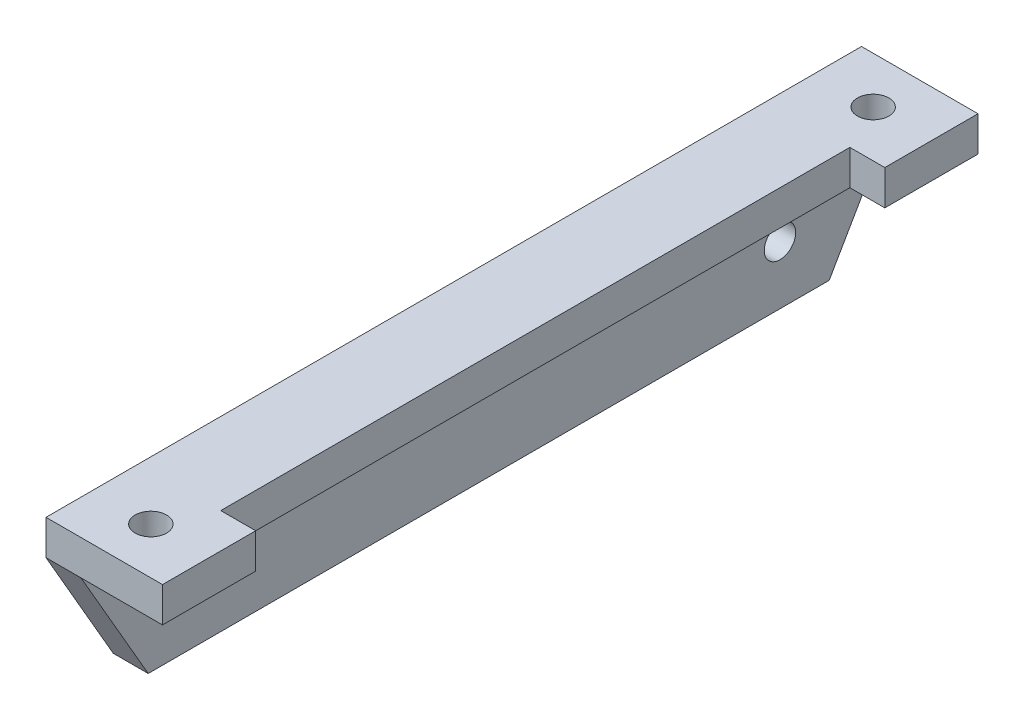
SolidWorks part; units mm, degrees
ref_plane "Front Plane" through (0, 0, 0) normal (0, 0, 1) x (1, 0, 0)
ref_plane "Top Plane" through (0, 0, 0) normal (0, 1, 0) x (1, 0, 0)
ref_plane "Right Plane" through (0, 0, 0) normal (1, 0, 0) x (0, 0, -1)
sketch "Sketch1" plane through (0, 0, 0) normal (0, 1, 0) x (1, 0, 0)
  line L1 (0, -35) -> (10, -35)
  line L2 (0, -35) -> (0, 35)
  line L3 (0, 35) -> (10, 35)
  line L4 (10, -35) -> (10, 35)
  point P4 (0, 0)
  dimension "D1" = 10
  dimension "D2" = 70
extrude "Boss-Extrude1" add sketch "Sketch1" along normal blind 3
sketch "Sketch2" plane through (0, 0, 0) normal (0, -1, 0) x (1, 0, 0)
  line L0 (10, -35) -> (0, -35) construction
  line L1 (0, 35) -> (3, 35)
  line L2 (0, 35) -> (0, -35)
  line L3 (0, -35) -> (3, -35)
  line L4 (3, 35) -> (3, -35)
  dimension "D1" = 3
extrude "Boss-Extrude2" add sketch "Sketch2" along normal blind 10
sketch "Sketch3" plane through (0, 3, 0) normal (0, 1, 0) x (1, 0, 0)
  line L0 (0, 35) -> (0, -35) construction
  circle A0 centre (5, 31) radius 1.35
  circle A1 centre (5, -31) radius 1.35
  dimension "D1" = 62
  dimension "D3" = 2.7
  dimension "D4" = 5
  dimension "D2" = 31
extrude "Cut-Extrude1" cut sketch "Sketch3" against normal through all both and the other way through all
sketch "Sketch4" plane through (3, 0, 0) normal (1, 0, 0) x (0, 0, -1)
  circle A0 centre (25, -5) radius 1.35
  circle A1 centre (-25, -5) radius 1.35
  dimension "D2" = 25
  dimension "D4" = 2.7
  dimension "D1" = 25
  dimension "D3" = 5
extrude "Cut-Extrude2" cut sketch "Sketch4" against normal blind 10
chamfer "Chamfer1" distance 10 angle 30 2 edges at (1.5, -10, -35) (1.5, -10, 35)
sketch "Sketch5" plane through (0, 3, 0) normal (0, 1, 0) x (1, 0, 0)
  line L0 (10, -35) -> (10, 35) construction
  line L1 (10, 27) -> (7, 27)
  line L2 (10, 27) -> (10, -27)
  line L3 (10, -27) -> (7, -27)
  line L4 (7, 27) -> (7, -27)
  circle A0 centre (5, 31) radius 1.35 construction
  circle A1 centre (5, -31) radius 1.35 construction
  dimension "D2" = 4
  dimension "D1" = 3
  dimension "D3" = 4
extrude "Cut-Extrude3" cut sketch "Sketch5" against normal blind 10
